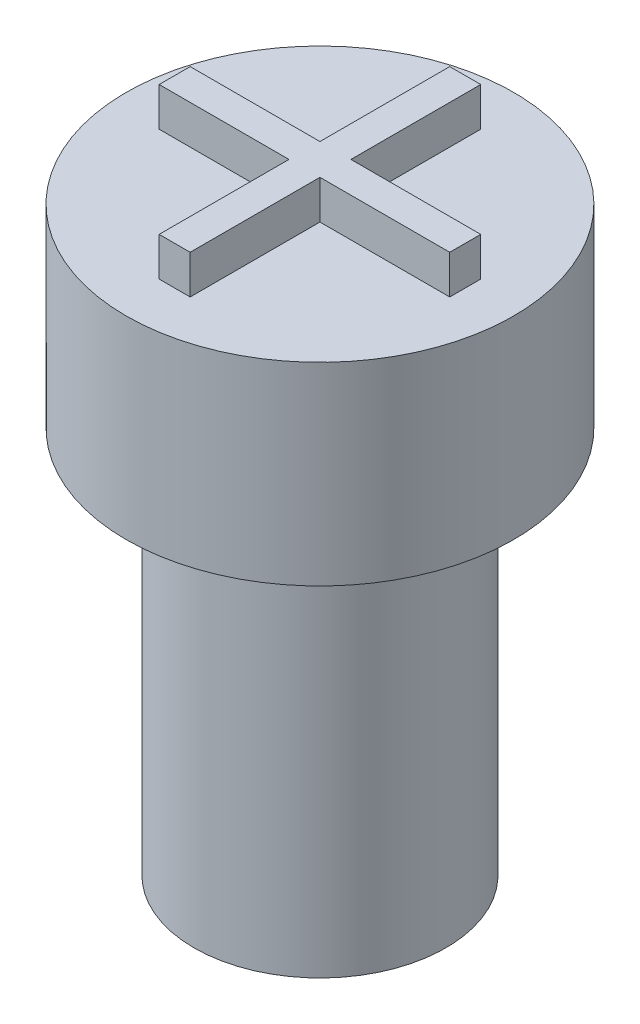
SolidWorks part; units mm, degrees
ref_plane "Front Plane" through (0, 0, 0) normal (0, 0, 1) x (1, 0, 0)
ref_plane "Top Plane" through (0, 0, 0) normal (0, 1, 0) x (1, 0, 0)
ref_plane "Right Plane" through (0, 0, 0) normal (1, 0, 0) x (0, 0, -1)
sketch "Sketch1" plane through (0, 0, 0) normal (0, 1, 0) x (1, 0, 0)
  circle A0 centre (0, 0) radius 3.25
  dimension "D1" = 6.5
extrude "Boss-Extrude1" add sketch "Sketch1" along normal blind 10 contours A0
sketch "Sketch2" plane through (0, 0, 0) normal (0, -1, 0) x (1, 0, 0)
  circle A1 centre (0, 0) radius 1.75
  dimension "D1" = 3.5
extrude "Cut-Extrude1" cut sketch "Sketch2" against normal blind 2.5
sketch "Sketch6" plane through (0, 10, 0) normal (0, 1, 0) x (1, 0, 0)
  circle A0 centre (0, 0) radius 5
  dimension "D1" = 10
extrude "Boss-Extrude2" add sketch "Sketch6" along normal blind 5 contours A0
sketch "Sketch7" plane through (0, 15, 0) normal (0, 1, 0) x (1, 0, 0)
  line L1 (-0.4, -3.75) -> (0.4, -3.75)
  line L2 (-0.4, -3.75) -> (-0.4, 3.75)
  line L3 (-0.4, 3.75) -> (0.4, 3.75)
  line L4 (0.4, -3.75) -> (0.4, 3.75)
  line L5 (-0.4, -3.75) -> (0.4, 3.75) construction
  line L6 (-0.4, 3.75) -> (0.4, -3.75) construction
  line L7 (-3.75, -0.4) -> (3.75, -0.4)
  line L8 (-3.75, -0.4) -> (-3.75, 0.4)
  line L9 (-3.75, 0.4) -> (3.75, 0.4)
  line L10 (3.75, -0.4) -> (3.75, 0.4)
  line L11 (-3.75, -0.4) -> (3.75, 0.4) construction
  line L12 (-3.75, 0.4) -> (3.75, -0.4) construction
  point P0 (0, 0)
  point P6 (0, 0)
  dimension "D1" = 0.8
  dimension "D2" = 7.5
  dimension "D3" = 7.5
  dimension "D4" = 0.8
sketch "Sketch8" plane through (0, 15, 0) normal (0, 1, 0) x (1, 0, 0)
  line L0 (0.4, 3.75) -> (-0.4, 3.75)
  line L1 (-0.4, 3.75) -> (-0.4, 0.4)
  line L2 (-0.4, -3.75) -> (-0.4, 3.75) construction
  line L3 (-3.75, 0.4) -> (3.75, 0.4) construction
  line L4 (-0.4, 0.4) -> (-3.75, 0.4)
  line L5 (-3.75, 0.4) -> (-3.75, -0.4)
  line L6 (-3.75, -0.4) -> (-0.4, -0.4)
  line L7 (-3.75, -0.4) -> (3.75, -0.4) construction
  line L8 (-0.4, -0.4) -> (-0.4, -3.75)
  line L9 (-0.4, -3.75) -> (0.4, -3.75)
  line L10 (0.4, -3.75) -> (0.4, -0.4)
  line L11 (0.4, -3.75) -> (0.4, 3.75) construction
  line L12 (0.4, -0.4) -> (3.75, -0.4)
  line L13 (3.75, -0.4) -> (3.75, 0.4)
  line L14 (3.75, 0.4) -> (0.4, 0.4)
  line L15 (0.4, 0.4) -> (0.4, 3.75)
extrude "Boss-Extrude3" add sketch "Sketch8" along normal blind 1
